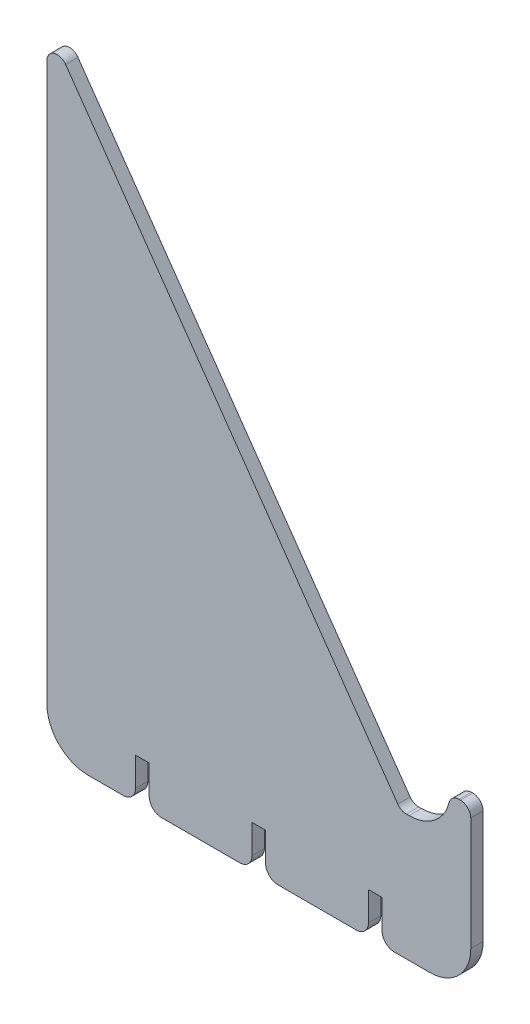
SolidWorks part; units mm, degrees
ref_plane "Front Plane" through (0, 0, 0) normal (0, 0, 1) x (1, 0, 0)
ref_plane "Top Plane" through (0, 0, 0) normal (0, 1, 0) x (1, 0, 0)
ref_plane "Right Plane" through (0, 0, 0) normal (1, 0, 0) x (0, 0, -1)
sketch "Sketch1" plane through (0, 0, 0) normal (0, 0, 1) x (1, 0, 0)
  line L1 (86.4963, -131.1793) -> (85.7977, -131.1793)
  line L2 (83.7498, -130.1133) -> (3.0077, -14.8016)
  line L3 (-0.8175, -9.3387) -> (79.4832, -124.02) construction
  line L4 (98.6297, -121.6843) -> (98.9835, -121.6843)
  line L6 (101.4835, -124.1843) -> (101.4835, -151.6843)
  line L7 (91.4835, -161.6843) -> (8.4598, -161.6843)
  line L8 (-1.5402, -151.6843) -> (-1.5402, -16.2355)
  arc A0 (96.203, -123.5833) -> (86.4963, -131.1793) centre (86.4963, -121.1793) cw
  arc A1 (101.4835, -151.6843) -> (91.4835, -161.6843) centre (91.4835, -151.6843) cw
  arc A2 (8.4598, -161.6843) -> (-1.5402, -151.6843) centre (8.4598, -151.6843) cw
  arc A3 (85.7977, -131.1793) -> (83.7498, -130.1133) centre (85.7977, -128.6793) cw
  arc A4 (98.9835, -121.6843) -> (101.4835, -124.1843) centre (98.9835, -124.1843) cw
  arc A5 (96.203, -123.5833) -> (98.6297, -121.6843) centre (98.6297, -124.1843) cw
  arc A6 (3.0077, -14.8016) -> (-1.5402, -16.2355) centre (0.9598, -16.2355) ccw
  point P8 (96.4963, -131.1793)
  point P14 (101.4835, -161.6843)
  point P19 (84.4963, -131.1793)
  point P22 (101.4835, -121.6843)
  point P25 (96.4835, -121.6843)
  point P28 (-1.5402, -8.3065)
  dimension "D3" = 10
  dimension "D6" = 10
  dimension "D7" = 2.5
  dimension "D8" = 2.5
  dimension "D1" = 150
  dimension "D2" = 12
  dimension "D4" = 40
  dimension "D5" = 5
extrude "Boss-Extrude1" add sketch "Sketch1" along normal blind 3
sketch "Sketch3" plane through (0, 0, 0) normal (0, 0, -1) x (-1, 0, 0)
  line L0 (-8.4598, -161.6843) -> (-91.4835, -161.6843) construction
  line L5 (-51.6217, -161.6843) -> (-51.6217, -151.6843)
  line L10 (-23.3217, -161.6843) -> (-20.0217, -161.6843)
  line L11 (-23.3217, -161.6843) -> (-23.3217, -151.6843)
  line L12 (-23.3217, -151.6843) -> (-20.0217, -151.6843)
  line L13 (-20.0217, -161.6843) -> (-20.0217, -151.6843)
  line L14 (-51.6217, -151.6843) -> (-48.3217, -151.6843)
  line L15 (-48.3217, -161.6843) -> (-48.3217, -151.6843)
  line L16 (-51.6217, -161.6843) -> (-48.3217, -161.6843)
  line L17 (-79.9217, -161.6843) -> (-79.9217, -151.6843)
  line L18 (-79.9217, -151.6843) -> (-76.6217, -151.6843)
  line L19 (-76.6217, -161.6843) -> (-76.6217, -151.6843)
  line L20 (-79.9217, -161.6843) -> (-76.6217, -161.6843)
  line L21 (-79.9217, -156.6843) -> (-101.4835, -156.6843) construction
  line L22 (-20.0217, -156.6843) -> (1.5402, -156.6843) construction
  line L23 (1.5402, -16.2355) -> (1.5402, -151.6843) construction
  line L24 (-101.4835, -151.6843) -> (-101.4835, -124.1843) construction
  line L25 (-76.6217, -156.6843) -> (-51.6217, -156.6843) construction
  line L26 (-51.6217, -156.6843) -> (-48.3217, -156.6843) construction
  line L27 (-48.3217, -156.6843) -> (-23.3217, -156.6843) construction
  dimension "D1" = 3.3
  dimension "D2" = 10
  dimension "D4" = 25
  dimension "D3" = 3
extrude "Cut-Extrude1" cut sketch "Sketch3" against normal through all
fillet "Fillet1" radius 3 6 edges at (20.0217, -161.6843, 1.5) (23.3217, -161.6843, 1.5) (48.3217, -161.6843, 1.5) (51.6217, -161.6843, 1.5) (76.6217, -161.6843, 1.5) (79.9217, -161.6843, 1.5)
